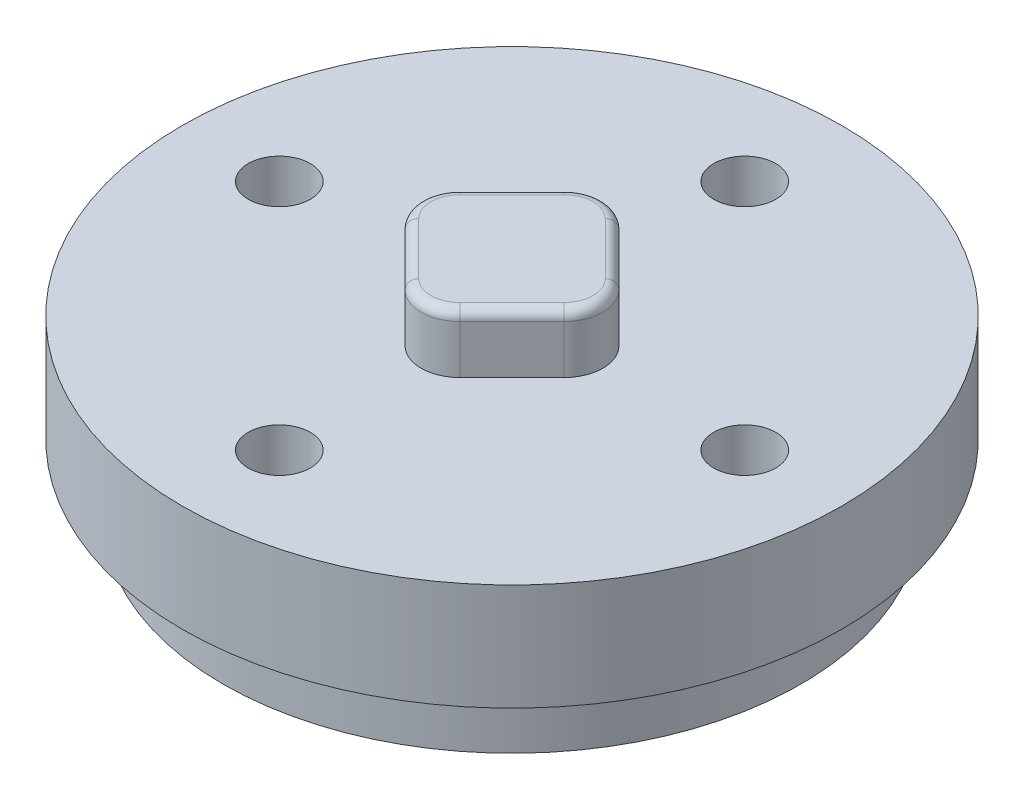
SolidWorks part; units mm, degrees
ref_plane "Front Plane" through (0, 0, 0) normal (0, 0, 1) x (1, 0, 0)
ref_plane "Top Plane" through (0, 0, 0) normal (0, 1, 0) x (1, 0, 0)
ref_plane "Right Plane" through (0, 0, 0) normal (1, 0, 0) x (0, 0, -1)
sketch "Sketch1" plane through (0, 0, 0) normal (0, 1, 0) x (1, 0, 0)
  circle A0 centre (3.5, 3.5) radius 1.5
  circle A1 centre (-3.5, -3.5) radius 1.5
  circle A2 centre (0, 0) radius 14.9
  circle A3 centre (0, 12) radius 1.6
  circle A4 centre (12, 0) radius 1.6
  circle A5 centre (0, -12) radius 1.6
  circle A6 centre (-12, 0) radius 1.6
  point P7 (0, 0)
  point P19 (0, 0)
  dimension "D1" = 3
  dimension "D5" = 29.8
  dimension "D6" = 3.2
  dimension "D2" = 3.5
  dimension "D3" = 3.5
  dimension "D7" = 12
  dimension "D4" = 2
  dimension "D8" = 4
extrude "Boss-Extrude1" add sketch "Sketch1" along normal blind 3.5 contours A2 A6 A5 A4 A3 A0 A1 | A1
sketch "Sketch2" plane through (0, 0, 0) normal (0, -1, 0) x (1, 0, 0)
  circle A0 centre (3.5, -3.5) radius 1.5 construction
  circle A1 centre (-3.5, 3.5) radius 1.5 construction
  circle A2 centre (3.5, -3.5) radius 1.5
  circle A3 centre (-3.5, 3.5) radius 1.5
extrude "Boss-Extrude2" add sketch "Sketch2" along normal blind 2
fillet "Fillet1" radius 0.3 2 edges at (3.5, -2, -5) (-3.5, -2, 2)
sketch "Sketch3" plane through (0, 3.5, 0) normal (0, 1, 0) x (1, 0, 0)
  circle A0 centre (0, 0) radius 17
  circle A1 centre (12, 0) radius 1.6 construction
  circle A2 centre (0, -12) radius 1.6 construction
  circle A3 centre (-12, 0) radius 1.6 construction
  circle A4 centre (0, 12) radius 1.6 construction
  circle A5 centre (12, 0) radius 1.6
  circle A6 centre (0, -12) radius 1.6
  circle A7 centre (-12, 0) radius 1.6
  circle A8 centre (0, 12) radius 1.6
  dimension "D1" = 34
extrude "Boss-Extrude3" add sketch "Sketch3" along normal blind 5.5
sketch "Sketch4" plane through (0, 9, 0) normal (0, 1, 0) x (1, 0, 0)
  line L0 (-4.1012, 1.4142) -> (-1.4142, 4.1012)
  line L1 (-4.1012, -1.4142) -> (-1.4142, -4.1012)
  line L2 (1.4142, 4.1012) -> (4.1012, 1.4142)
  line L3 (1.4142, -4.1012) -> (4.1012, -1.4142)
  line L4 (-5.5154, 0) -> (5.5154, 0) construction
  line L5 (0, 5.5154) -> (0, -5.5154) construction
  arc A0 (4.1012, 1.4142) -> (4.1012, -1.4142) centre (2.687, 0) cw
  arc A1 (-1.4142, -4.1012) -> (1.4142, -4.1012) centre (0, -2.687) ccw
  arc A2 (-4.1012, -1.4142) -> (-4.1012, 1.4142) centre (-2.687, 0) cw
  arc A3 (-1.4142, 4.1012) -> (1.4142, 4.1012) centre (0, 2.687) cw
  point P1 (0, 0)
  dimension "D2" = 2
  dimension "D1" = 7.8
extrude "Boss-Extrude4" add sketch "Sketch4" along normal blind 3
fillet "Fillet2" radius 0.5 8 edges at (0, 12, 4.687) (-2.7577, 12, 2.7577) (-4.687, 12, 0) (-2.7577, 12, -2.7577) (0, 12, -4.687) (2.7577, 12, -2.7577) (4.687, 12, 0) (2.7577, 12, 2.7577)
